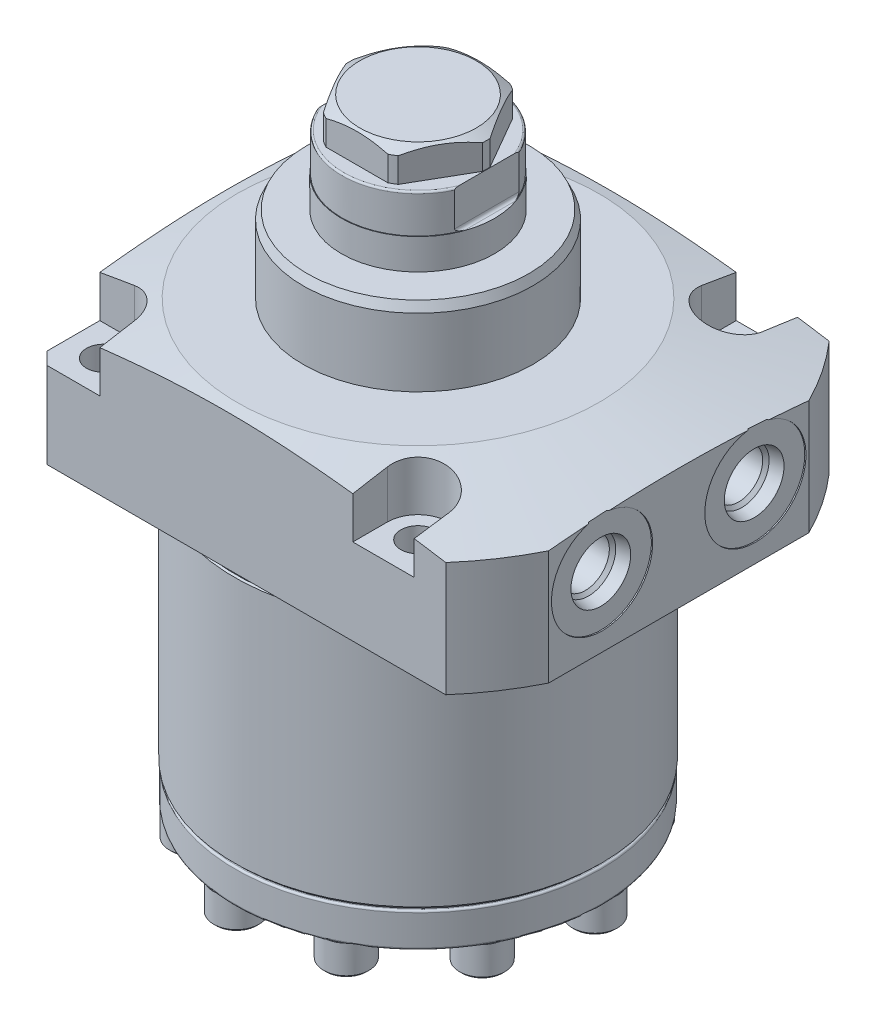
SolidWorks part; units mm, degrees
material "Alloy Steel"
ref_plane "Front Plane" through (0, 0, 0) normal (0, 0, 1) x (1, 0, 0)
ref_plane "Top Plane" through (0, 0, 0) normal (0, 1, 0) x (1, 0, 0)
ref_plane "Right Plane" through (0, 0, 0) normal (1, 0, 0) x (0, 0, -1)
sketch "Sketch1" plane through (0, 0, 0) normal (0, 0, 1) x (1, 0, 0)
  line L0 (0, -54.5338) -> (60.325, -54.5338)
  line L1 (60.325, -54.5338) -> (60.325, 28.575)
  line L2 (60.325, 28.575) -> (0, 28.575)
  line L3 (0, 28.575) -> (0, -54.5338)
  line L4 (0, 32.6238) -> (0, -56.449) construction
  dimension "D1" = 28.575
  dimension "D2" = 120.65
  dimension "D3" = 83.1088
revolve "Revolve1" add sketch "Sketch1" angle 360 about L4
sketch "Sketch2" plane through (0, 0, 0) normal (0, 0, 1) x (1, 0, 0)
  line L0 (63.5, 0) -> (63.5, -54.5338)
  line L1 (63.5, -54.5338) -> (37.973, -54.5338)
  line L2 (63.5, 0) -> (37.6555, 0)
  line L3 (37.6555, 0) -> (37.6555, -2.2225)
  line L4 (37.6555, -2.2225) -> (37.973, -2.54)
  line L5 (37.973, -2.54) -> (37.973, -54.5338)
  line L6 (0, 2.62) -> (0, -55.0202) construction
  line L7 (-60.325, -54.5338) -> (60.325, -54.5338) construction
  dimension "D1" = 75.946
  dimension "D2" = 45
  dimension "D3" = 75.311
  dimension "D4" = 2.2225
  dimension "D5" = 54.5338
  dimension "D6" = 127
revolve "Cut-Revolve1" cut sketch "Sketch2" angle 360 about L6
sketch "Sketch4" plane through (0, 28.575, 0) normal (0, 1, 0) x (0, 0, -1)
  line L0 (-39.6875, 39.7002) -> (39.6875, 39.7002)
  line L1 (39.6875, 39.7002) -> (39.6875, -53.975)
  line L2 (39.6875, -53.975) -> (-39.6875, -53.975)
  line L3 (-39.6875, -53.975) -> (-39.6875, 39.7002)
  line L4 (0, 32.2516) -> (0, -48.6347) construction
  line L5 (0, 0) -> (20.7547, 0) construction
  dimension "D1" = 79.375
  dimension "D2" = 53.975
  dimension "D3" = 93.6752
extrude "Cut-Extrude26" cut sketch "Sketch4" against normal through all flip side to cut
sketch "Sketch5" plane through (0, 0, 0) normal (0, 0, 1) x (1, 0, 0)
  line L0 (37.465, 28.575) -> (76.2, 20.3416)
  line L1 (0, 28.8261) -> (0, -19.0517) construction
  line L2 (-39.7002, 28.575) -> (45.4314, 28.575) construction
  line L3 (76.2, 20.3416) -> (76.2, 28.575)
  line L4 (76.2, 28.575) -> (37.465, 28.575)
  dimension "D1" = 12
  dimension "D2" = 74.93
  dimension "D3" = 76.2
revolve "Cut-Revolve2" cut sketch "Sketch5" angle 360 about L1
hole_wizard "Hole1" positions "Sketch64" profile "Sketch63" legacy end condition through all
sketch "Sketch64" plane through (0, 0, 0) normal (0, -1, 0) x (1, 0, 0)
  line L0 (0, 0) -> (0, 36.8385) construction
  line L1 (0, 0) -> (33.6753, 0) construction
  point P0 (32.5374, 32.5374)
  dimension "D1" = 32.5374
  dimension "D2" = 32.5374
sketch "Sketch63" plane through (32.5374, 0, 32.5374) normal (1, 0, 0) x (0, 0, -1)
  line L0 (0, 0) -> (0, 28.575)
  line L1 (0, 28.575) -> (3.5687, 28.575)
  line L2 (3.5687, 28.575) -> (3.5687, 0)
  line L3 (3.5687, 0) -> (0, 0)
  line L4 (0, 110) -> (0, -10) construction
  dimension "Diameter" = 7.1374
  dimension "Depth" = 28.575
pattern_circular "CirPattern1" count 4 over 360 about axis through (0, 0, 0) along (0, 1, 0) of "Hole1"
sketch "Sketch9" plane through (0, 28.575, 0) normal (0, 1, 0) x (0, 0, -1)
  line L0 (26.1874, 39.7002) -> (39.6875, 39.7002)
  line L1 (39.6875, 39.7002) -> (39.6875, 26.1874)
  line L2 (26.1874, 32.5374) -> (26.1874, 39.7002)
  line L3 (32.5374, 26.1874) -> (39.6875, 26.1874)
  line L4 (39.6875, 39.7002) -> (39.6875, -45.4314) construction
  line L5 (-39.6875, 39.7002) -> (39.6875, 39.7002) construction
  line L6 (0, 0) -> (0, 50.6442) construction
  line L7 (32.5374, -26.1874) -> (39.6875, -26.1874)
  line L8 (39.6875, -26.1874) -> (39.6875, -38.8874)
  line L9 (39.6875, -38.8874) -> (32.5374, -38.8874)
  line L11 (-39.6875, -38.8874) -> (-32.5374, -38.8874)
  line L12 (-39.6875, -26.1874) -> (-39.6875, -38.8874)
  line L13 (-32.5374, -26.1874) -> (-39.6875, -26.1874)
  line L14 (-32.5374, 26.1874) -> (-39.6875, 26.1874)
  line L15 (-26.1874, 32.5374) -> (-26.1874, 39.7002)
  line L16 (-39.6875, 39.7002) -> (-39.6875, 26.1874)
  line L17 (-26.1874, 39.7002) -> (-39.6875, 39.7002)
  arc A0 (26.1874, 32.5374) -> (32.5374, 26.1874) centre (32.5374, 32.5374) ccw
  circle A1 centre (32.5374, 32.5374) radius 3.5687 construction
  arc A2 (32.5374, -26.1874) -> (32.5374, -38.8874) centre (32.5374, -32.5374) ccw
  arc A3 (-32.5374, -26.1874) -> (-32.5374, -38.8874) centre (-32.5374, -32.5374) cw
  arc A4 (-26.1874, 32.5374) -> (-32.5374, 26.1874) centre (-32.5374, 32.5374) cw
  dimension "D1" = 6.35
  dimension "D2" = 6.35
extrude "Cut-Extrude27" cut sketch "Sketch9" against normal offset from surface (10.795 mm away) 17.78 up to face at (-32.5374, 0, 28.9687)
ref_plane "Plane63" through (0, 0, -15.875) normal (0, 0, 1) x (1, 0, 0)
sketch "S2D0007" plane through (0, 0, -15.875) normal (0, 0, 1) x (1, 0, 0)
  line L0 (53.975, 14.3002) -> (53.975, 3.8227)
  line L1 (53.975, 3.8227) -> (53.721, 3.8227)
  line L2 (53.721, 3.8227) -> (53.721, 8.1153)
  line L3 (53.721, 8.1153) -> (51.1683, 8.6579)
  line L4 (51.1683, 8.6579) -> (50.5044, 9.3218)
  line L5 (50.5044, 9.3218) -> (38.989, 9.3218)
  line L6 (38.989, 9.3218) -> (38.989, 14.3002)
  line L7 (38.989, 14.3002) -> (53.975, 14.3002)
  line L8 (0, 14.3002) -> (19.3374, 14.3002) construction
  line L10 (45.4314, 0) -> (-39.7002, 0) construction
  line L11 (53.975, 23.716) -> (53.975, 0) construction
  dimension "D1" = 0.254
  dimension "D2" = 14.3002
  dimension "D3" = 9.9568
  dimension "D4" = 14.986
  dimension "D5" = 20.955
  dimension "D6" = 45
  dimension "D7" = 12
  dimension "D8" = 12.3698
  dimension "D9" = 2.5527
revolve "Cut-Revolve3" cut sketch "S2D0007" angle 360 about L8
mirror "Mirror1" about plane through (0, 0, 0) normal (0, 0, 1) of "Cut-Revolve3"
ref_plane "Plane64" through (0, 0, -19.05) normal (0, 0, 1) x (1, 0, 0)
sketch "S2D0013" plane through (34.544, 0, -19.05) normal (0, 0, 1) x (-1, 0, 0)
  line L0 (-9.906, 0) -> (-9.906, -12.7)
  line L1 (-9.906, -12.7) -> (-8.6614, -12.7)
  line L2 (-8.6614, -12.7) -> (-8.6614, -3.3528)
  line L3 (-8.6614, -3.3528) -> (-6.5278, -3.3528)
  line L4 (-6.5278, -3.3528) -> (-6.5278, -1.3208)
  line L5 (-6.5278, -1.3208) -> (-4.3307, -1.3208)
  line L6 (-4.3307, -1.3208) -> (-4.3307, 0)
  line L7 (-4.3307, 0) -> (-9.906, 0)
  line L8 (-9.906, -18.7284) -> (-9.906, 0.635) construction
  line L9 (34.544, 54.5338) -> (34.544, 2.54) construction
  line L10 (-10.8874, 0) -> (74.2442, 0) construction
  dimension "D1" = 12.7
  dimension "D2" = 2.032
  dimension "D3" = 44.45
  dimension "D4" = 11.1506
  dimension "D5" = 6.7564
  dimension "D6" = 1.3208
  dimension "D7" = 2.4892
revolve "Cut-Revolve4" cut sketch "S2D0013" angle 360 about L8
sketch "Sketch22" plane through (0, 0, 0) normal (0, 0, 1) x (1, 0, 0)
  line L0 (0, 28.575) -> (0, 44.45)
  line L1 (0, 44.45) -> (22.9771, 44.45)
  line L2 (22.9771, 44.45) -> (23.8062, 42.672)
  line L3 (23.8062, 42.672) -> (23.8062, 28.575)
  line L4 (23.8062, 28.575) -> (0, 28.575)
  line L5 (0, 27.7812) -> (0, 55.8206) construction
  line L6 (37.465, 28.575) -> (-37.465, 28.575) construction
  line L7 (0, 0) -> (0, 23.716) construction
  line L8 (45.4314, 0) -> (-39.7002, 0) construction
  dimension "D1" = 47.6123
  dimension "D2" = 25
  dimension "D3" = 44.45
  dimension "D4" = 1.778
revolve "Revolve4" add sketch "Sketch22" angle 360 about L5
sketch "S2D0005" plane through (0, 0, 0) normal (0, 0, 1) x (1, 0, 0)
  line L0 (0, 28.575) -> (15.8623, 28.575)
  line L1 (15.8623, 28.575) -> (15.8623, 50.8)
  line L2 (15.8623, 50.8) -> (15.7353, 50.8)
  line L3 (15.7353, 50.8) -> (15.7353, 58.3692)
  line L4 (15.3543, 58.7502) -> (14.1605, 58.7502)
  line L5 (0, 43.1013) -> (0, 89.7556) construction
  line L6 (0, 0) -> (0, 23.716) construction
  line L9 (0, 65.1002) -> (12.065, 65.1002)
  line L10 (12.065, 65.1002) -> (14.1605, 63.8904)
  line L11 (14.1605, 63.8904) -> (14.1605, 58.7502)
  line L13 (-39.7002, 0) -> (45.4314, 0) construction
  line L15 (37.465, 28.575) -> (-37.465, 28.575) construction
  line L16 (0, 65.1002) -> (0, 28.575)
  arc A0 (15.7353, 58.3692) -> (15.3543, 58.7502) centre (15.3543, 58.3692) ccw
  dimension "D6" = 0.381
  dimension "D1" = 28.321
  dimension "D2" = 65.1002
  dimension "D3" = 30
  dimension "D4" = 24.13
  dimension "D5" = 6.35
  dimension "D7" = 31.4706
  dimension "D8" = 31.7246
  dimension "D9" = 7.9502
revolve "Revolve2" add sketch "S2D0005" angle 360 about L5
sketch "Sketch66" plane through (0, 65.1002, 0) normal (0, 1, 0) x (1, 0, 0)
  line L1 (14.5914, 0) -> (7.2957, 12.6365)
  line L2 (7.2957, 12.6365) -> (-7.2957, 12.6365)
  line L3 (-7.2957, 12.6365) -> (-14.5914, 0)
  line L4 (-14.5914, 0) -> (-7.2957, -12.6365)
  line L5 (-7.2957, -12.6365) -> (7.2957, -12.6365)
  line L6 (7.2957, -12.6365) -> (14.5914, 0)
  circle A0 centre (0, 0) radius 12.6365 construction
  dimension "D1" = 25.273
extrude "Cut-Extrude28" cut sketch "Sketch66" against normal up to surface (6.35 mm away) flip side to cut up to face at (14.1605, 58.7502, 0)
sketch "Sketch28" plane through (0, 0, 0) normal (0, 0, 1) x (1, 0, 0)
  line L0 (14.2494, 58.7502) -> (15.7353, 58.7502)
  line L1 (15.7353, 50.8) -> (15.7353, 58.7502)
  line L2 (14.2494, 58.7502) -> (14.2494, 51.435)
  line L3 (14.8844, 50.8) -> (15.7353, 50.8)
  line L4 (0, 58.3692) -> (0, 50.8) construction
  line L5 (15.8623, 50.8) -> (-15.8623, 50.8) construction
  line L6 (15.7353, 50.8) -> (15.7353, 58.3692) construction
  line L7 (15.3543, 58.7502) -> (-15.3543, 58.7502) construction
  line L8 (0, 66.6242) -> (0, 77.8736) construction
  line L9 (-14.8844, 50.8) -> (-15.7353, 50.8)
  line L10 (-14.2494, 58.7502) -> (-14.2494, 51.435)
  line L11 (-15.7353, 50.8) -> (-15.7353, 58.7502)
  line L12 (-14.2494, 58.7502) -> (-15.7353, 58.7502)
  arc A0 (-14.2494, 51.435) -> (-14.8844, 50.8) centre (-14.8844, 51.435) cw
  arc A1 (14.2494, 51.435) -> (14.8844, 50.8) centre (14.8844, 51.435) ccw
  dimension "D3" = 0.635
  dimension "D2" = 28.4988
extrude "Cut-Extrude4" cut sketch "Sketch28" against normal mid plane 25.4
sketch "Sketch29" plane through (34.544, 0, -19.05) normal (0, 0, -1) x (-1, 0, 0)
  line L0 (-9.906, 3.3528) -> (-6.6675, 3.3528)
  line L1 (-6.6675, 3.3528) -> (-6.6675, 2.0574)
  line L2 (-6.6675, 2.0574) -> (-7.0612, 2.0574)
  line L3 (-7.0612, 2.0574) -> (-7.0612, 1.8157)
  line L4 (-8.4705, 0.4064) -> (-9.906, 0.4064)
  line L5 (-9.906, 0.4064) -> (-9.906, 3.3528)
  line L6 (-9.906, 3.5001) -> (-9.906, -0.842) construction
  line L7 (-9.906, 3.3528) -> (-9.906, 10.7283) construction
  line L8 (-9.906, 0) -> (-9.906, 1.3208) construction
  line L9 (-13.2842, 3.3528) -> (-6.5278, 3.3528) construction
  arc A0 (-7.0612, 1.8157) -> (-8.4705, 0.4064) centre (-8.4705, 1.8157) cw
  dimension "D5" = 1.4093
  dimension "D1" = 1.651
  dimension "D2" = 6.477
  dimension "D3" = 1.2954
  dimension "D4" = 5.6896
revolve "Revolve3" add sketch "Sketch29" angle 360 about L6
sketch "Sketch31" plane through (0, 0.4064, 0) normal (0, -1, 0) x (1, 0, 0)
  line L1 (43.8726, -20.05) -> (45.0274, -20.05)
  line L2 (45.0274, -20.05) -> (45.6047, -19.05)
  line L3 (45.6047, -19.05) -> (45.0274, -18.05)
  line L4 (45.0274, -18.05) -> (43.8726, -18.05)
  line L5 (43.8726, -18.05) -> (43.2953, -19.05)
  line L6 (43.2953, -19.05) -> (43.8726, -20.05)
  circle A0 centre (44.45, -19.05) radius 1 construction
  dimension "D1" = 2
extrude "Cut-Extrude6" cut sketch "Sketch31" against normal blind 0.9906
sketch "Sketch32" plane through (34.544, 0, -19.05) normal (0, 0, -1) x (-1, 0, 0)
  line L0 (-9.906, -7.6689) -> (-9.906, 1.4097) construction
  line L2 (-9.906, 1.3208) -> (-9.906, 3.3528) construction
  line L3 (-3.1115, 0) -> (72.1995, 0) construction
  circle A0 centre (-5.1943, 0.4318) radius 0.889
  dimension "D1" = 1.778
  dimension "D2" = 0.4318
  dimension "D3" = 9.4234
revolve "Revolve6" add sketch "Sketch32" angle 360 about L0
sketch "Sketch67" plane through (0, 0, 0) normal (0, -1, 0) x (1, 0, 0)
  line L0 (0, 0) -> (48.8266, 0) construction
  point P0 (44.45, -19.05)
  point P6 (44.45, 19.05)
pattern_sketch "Sketch-Pattern1" of "Cut-Revolve4", "Revolve3", "Cut-Extrude6" driven by "Sketch67"
pattern_sketch "Sketch-Pattern2" [suppressed]
chamfer "Chamfer1" distance 0.762 angle 45 1 edges at (-37.973, -54.5338, 0)
chamfer "Chamfer2" distance 2.54 angle 45 2 edges at (-39.7002, 8.89, -39.6875) (-39.7002, 8.89, 39.6875)
fillet "Fillet3" radius 0.508 1 edges at (-37.6555, 0, 0)
sketch "Sketch69" plane through (0, 0, 0) normal (0, 0, 1) x (1, 0, 0)
  line L0 (0, 0) -> (0, -66.9582) construction
  line L1 (0, -54.5338) -> (37.465, -54.5338)
  line L3 (37.846, -54.9148) -> (37.846, -61.214)
  line L4 (37.465, -61.595) -> (27.813, -61.595)
  line L5 (27.432, -61.976) -> (27.432, -67.818)
  line L6 (27.051, -68.199) -> (0, -68.199)
  line L7 (0, -68.199) -> (0, -54.5338)
  line L8 (-37.211, -54.5338) -> (37.211, -54.5338) construction
  arc A0 (27.432, -67.818) -> (27.051, -68.199) centre (27.051, -67.818) cw
  arc A1 (27.813, -61.595) -> (27.432, -61.976) centre (27.813, -61.976) ccw
  arc A2 (37.846, -61.214) -> (37.465, -61.595) centre (37.465, -61.214) cw
  arc A3 (37.846, -54.9148) -> (37.465, -54.5338) centre (37.465, -54.9148) ccw
  point P17 (37.846, -61.595)
  point P20 (37.846, -54.5338)
  dimension "D5" = 0.381
  dimension "D1" = 13.6652
  dimension "D2" = 54.864
  dimension "D3" = 7.0612
  dimension "D4" = 75.692
revolve "Revolve9" add sketch "Sketch69" angle 360 about L0
sketch "Sketch70" plane through (0, -61.595, 0) normal (0, -1, 0) x (1, 0, 0)
  line L0 (0, 0) -> (72.6449, 0) construction
  line L1 (0, 0) -> (4.2056, -0.4792) construction
  circle A0 centre (0, 0) radius 33.0835 construction
  circle A1 centre (32.8708, -3.7452) radius 4.699
  circle A2 centre (0, 0) radius 27.051 construction
  dimension "D1" = 66.167
  dimension "D3" = 9.398
  dimension "D2" = 6.5
extrude "Extrude7" add sketch "Sketch70" along normal blind 6.35
sketch "Sketch71" plane through (0, -67.945, 0) normal (0, -1, 0) x (1, 0, 0)
  line L1 (34.2456, -6.1264) -> (35.6205, -3.7452)
  line L2 (35.6205, -3.7452) -> (34.2456, -1.3639)
  line L3 (34.2456, -1.3639) -> (31.496, -1.3639)
  line L4 (31.496, -1.3639) -> (30.1212, -3.7452)
  line L5 (30.1212, -3.7452) -> (31.496, -6.1264)
  line L6 (31.496, -6.1264) -> (34.2456, -6.1264)
  circle A0 centre (32.8708, -3.7452) radius 2.3812 construction
  circle A2 centre (32.8708, -3.7452) radius 4.699 construction
  dimension "D1" = 4.7625
extrude "Cut-Extrude30" cut sketch "Sketch71" against normal blind 3.048
chamfer "Chamfer3" distance 0.508 angle 45 1 edges at (37.5698, -67.945, -3.7452)
pattern_circular "CirPattern4" count 10 every 35 about axis through (0, 0, 0) along (0, 1, 0) of "Chamfer3", "Cut-Extrude30", "Extrude7"
